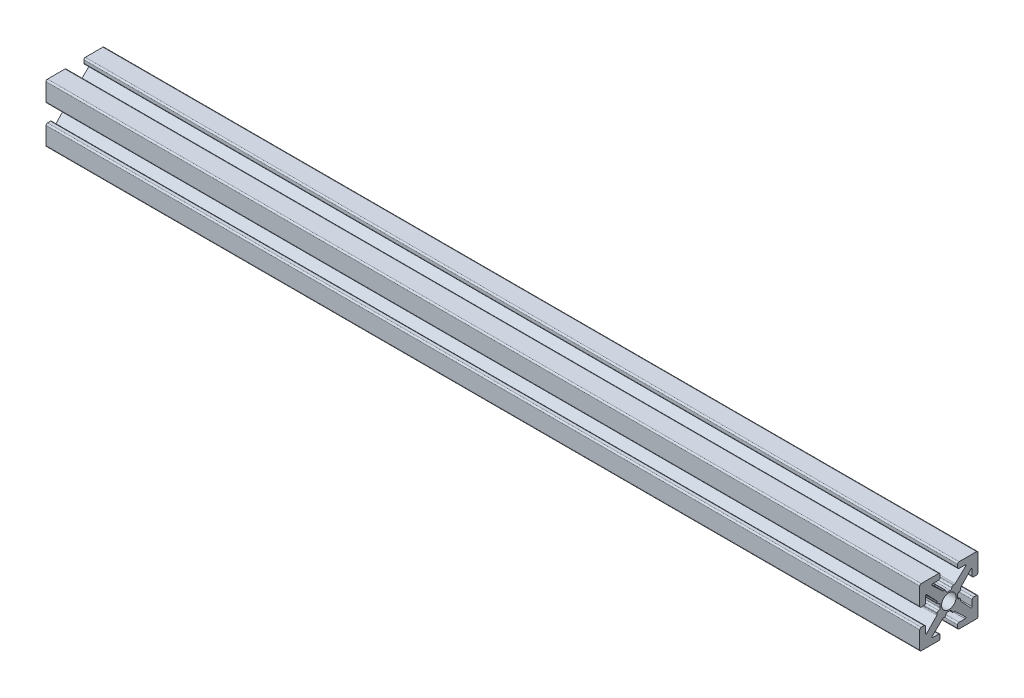
SolidWorks part; units mm, degrees
material "1060 Сплав"
ref_plane "Front Plane" through (0, 0, 0) normal (0, 0, 1) x (1, 0, 0)
ref_plane "Top Plane" through (0, 0, 0) normal (0, 1, 0) x (1, 0, 0)
ref_plane "Right Plane" through (0, 0, 0) normal (1, 0, 0) x (0, 0, -1)
sketch "Sketch1" plane through (0, 0, 0) normal (1, 0, 0) x (0, 0, -1)
  line L0 (0, 0) -> (0, 1.4948) construction
  line L1 (-0.2413, 1.4948) -> (0.2413, 1.4948)
  line L2 (5, 1.7526) -> (5, 4.746)
  line L3 (0.7493, 2.0028) -> (0.8899, 2.0028)
  line L4 (1.0639, 2.0718) -> (2.8908, 3.7899)
  line L5 (2.8038, 4.0094) -> (1.7526, 4.0094)
  line L6 (1.4986, 4.2634) -> (1.4986, 4.746)
  line L7 (1.7526, 5) -> (4.746, 5)
  line L8 (5, 5) -> (0, 0) construction
  line L9 (0, 0) -> (8.6271, 0) construction
  line L10 (0, 0) -> (0, 5) construction
  line L11 (4.2634, 1.4986) -> (4.746, 1.4986)
  line L12 (4.0094, 2.8038) -> (4.0094, 1.7526)
  line L13 (2.0718, 1.0639) -> (3.7899, 2.8908)
  line L14 (2.0028, 0.7493) -> (2.0028, 0.8899)
  line L15 (1.4948, -0.2413) -> (1.4948, 0.2413)
  line L16 (0, 0) -> (1.4948, 0) construction
  line L17 (-0.2413, -1.4948) -> (0.2413, -1.4948)
  line L18 (0.7493, -2.0028) -> (0.8899, -2.0028)
  line L19 (1.0639, -2.0718) -> (2.8908, -3.7899)
  line L20 (2.8038, -4.0094) -> (1.7526, -4.0094)
  line L21 (1.4986, -4.2634) -> (1.4986, -4.746)
  line L22 (1.7526, -5) -> (4.746, -5)
  line L23 (5, -1.7526) -> (5, -4.746)
  line L24 (4.2634, -1.4986) -> (4.746, -1.4986)
  line L25 (4.0094, -2.8038) -> (4.0094, -1.7526)
  line L26 (2.0718, -1.0639) -> (3.7899, -2.8908)
  line L27 (2.0028, -0.7493) -> (2.0028, -0.8899)
  line L28 (-0.7493, 2.0028) -> (-0.8899, 2.0028)
  line L29 (-1.0639, 2.0718) -> (-2.8908, 3.7899)
  line L30 (-2.8038, 4.0094) -> (-1.7526, 4.0094)
  line L31 (-1.4986, 4.2634) -> (-1.4986, 4.746)
  line L32 (-1.7526, 5) -> (-4.746, 5)
  line L33 (-5, 1.7526) -> (-5, 4.746)
  line L34 (-4.2634, 1.4986) -> (-4.746, 1.4986)
  line L35 (-4.0094, 2.8038) -> (-4.0094, 1.7526)
  line L36 (-2.0718, 1.0639) -> (-3.7899, 2.8908)
  line L37 (-2.0028, 0.7493) -> (-2.0028, 0.8899)
  line L38 (-1.4948, -0.2413) -> (-1.4948, 0.2413)
  line L39 (-2.0028, -0.7493) -> (-2.0028, -0.8899)
  line L40 (-2.0718, -1.0639) -> (-3.7899, -2.8908)
  line L41 (-4.0094, -2.8038) -> (-4.0094, -1.7526)
  line L42 (-4.2634, -1.4986) -> (-4.746, -1.4986)
  line L43 (-5, -1.7526) -> (-5, -4.746)
  line L44 (-1.7526, -5) -> (-4.746, -5)
  line L45 (-1.4986, -4.2634) -> (-1.4986, -4.746)
  line L46 (-2.8038, -4.0094) -> (-1.7526, -4.0094)
  line L47 (-1.0639, -2.0718) -> (-2.8908, -3.7899)
  line L48 (-0.7493, -2.0028) -> (-0.8899, -2.0028)
  arc A0 (2.8908, 3.7899) -> (2.8038, 4.0094) centre (2.8038, 3.8824) ccw
  arc A1 (0.4953, 1.7488) -> (0.7493, 2.0028) centre (0.7493, 1.7488) cw
  arc A2 (0.8899, 2.0028) -> (1.0639, 2.0718) centre (0.8899, 2.2568) ccw
  arc A3 (1.7526, 4.0094) -> (1.4986, 4.2634) centre (1.7526, 4.2634) cw
  arc A4 (1.4986, 4.746) -> (1.7526, 5) centre (1.7526, 4.746) cw
  arc A5 (0.2413, 1.4948) -> (0.4953, 1.7488) centre (0.2413, 1.7488) ccw
  arc A6 (4.746, 1.4986) -> (5, 1.7526) centre (4.746, 1.7526) ccw
  arc A7 (4.0094, 1.7526) -> (4.2634, 1.4986) centre (4.2634, 1.7526) ccw
  arc A8 (3.7899, 2.8908) -> (4.0094, 2.8038) centre (3.8824, 2.8038) cw
  arc A9 (2.0028, 0.8899) -> (2.0718, 1.0639) centre (2.2568, 0.8899) cw
  arc A10 (1.7488, 0.4953) -> (2.0028, 0.7493) centre (1.7488, 0.7493) ccw
  arc A11 (1.4948, 0.2413) -> (1.7488, 0.4953) centre (1.7488, 0.2413) cw
  arc A12 (0.2413, -1.4948) -> (0.4953, -1.7488) centre (0.2413, -1.7488) cw
  arc A13 (0.4953, -1.7488) -> (0.7493, -2.0028) centre (0.7493, -1.7488) ccw
  arc A14 (0.8899, -2.0028) -> (1.0639, -2.0718) centre (0.8899, -2.2568) cw
  arc A15 (2.8908, -3.7899) -> (2.8038, -4.0094) centre (2.8038, -3.8824) cw
  arc A16 (1.7526, -4.0094) -> (1.4986, -4.2634) centre (1.7526, -4.2634) ccw
  arc A17 (1.4986, -4.746) -> (1.7526, -5) centre (1.7526, -4.746) ccw
  arc A18 (4.746, -1.4986) -> (5, -1.7526) centre (4.746, -1.7526) cw
  arc A19 (4.0094, -1.7526) -> (4.2634, -1.4986) centre (4.2634, -1.7526) cw
  arc A20 (3.7899, -2.8908) -> (4.0094, -2.8038) centre (3.8824, -2.8038) ccw
  arc A21 (2.0028, -0.8899) -> (2.0718, -1.0639) centre (2.2568, -0.8899) ccw
  arc A22 (1.7488, -0.4953) -> (2.0028, -0.7493) centre (1.7488, -0.7493) cw
  arc A23 (1.4948, -0.2413) -> (1.7488, -0.4953) centre (1.7488, -0.2413) ccw
  arc A24 (-0.2413, 1.4948) -> (-0.4953, 1.7488) centre (-0.2413, 1.7488) cw
  arc A25 (-0.4953, 1.7488) -> (-0.7493, 2.0028) centre (-0.7493, 1.7488) ccw
  arc A26 (-0.8899, 2.0028) -> (-1.0639, 2.0718) centre (-0.8899, 2.2568) cw
  arc A27 (-2.8908, 3.7899) -> (-2.8038, 4.0094) centre (-2.8038, 3.8824) cw
  arc A28 (-1.7526, 4.0094) -> (-1.4986, 4.2634) centre (-1.7526, 4.2634) ccw
  arc A29 (-1.4986, 4.746) -> (-1.7526, 5) centre (-1.7526, 4.746) ccw
  arc A30 (-4.746, 1.4986) -> (-5, 1.7526) centre (-4.746, 1.7526) cw
  arc A31 (-4.0094, 1.7526) -> (-4.2634, 1.4986) centre (-4.2634, 1.7526) cw
  arc A32 (-3.7899, 2.8908) -> (-4.0094, 2.8038) centre (-3.8824, 2.8038) ccw
  arc A33 (-2.0028, 0.8899) -> (-2.0718, 1.0639) centre (-2.2568, 0.8899) ccw
  arc A34 (-1.7488, 0.4953) -> (-2.0028, 0.7493) centre (-1.7488, 0.7493) cw
  arc A35 (-1.4948, 0.2413) -> (-1.7488, 0.4953) centre (-1.7488, 0.2413) ccw
  arc A36 (-1.4948, -0.2413) -> (-1.7488, -0.4953) centre (-1.7488, -0.2413) cw
  arc A37 (-1.7488, -0.4953) -> (-2.0028, -0.7493) centre (-1.7488, -0.7493) ccw
  arc A38 (-2.0028, -0.8899) -> (-2.0718, -1.0639) centre (-2.2568, -0.8899) cw
  arc A39 (-3.7899, -2.8908) -> (-4.0094, -2.8038) centre (-3.8824, -2.8038) cw
  arc A40 (-4.0094, -1.7526) -> (-4.2634, -1.4986) centre (-4.2634, -1.7526) ccw
  arc A41 (-4.746, -1.4986) -> (-5, -1.7526) centre (-4.746, -1.7526) ccw
  arc A42 (-1.4986, -4.746) -> (-1.7526, -5) centre (-1.7526, -4.746) cw
  arc A43 (-1.7526, -4.0094) -> (-1.4986, -4.2634) centre (-1.7526, -4.2634) cw
  arc A44 (-2.8908, -3.7899) -> (-2.8038, -4.0094) centre (-2.8038, -3.8824) ccw
  arc A45 (-0.8899, -2.0028) -> (-1.0639, -2.0718) centre (-0.8899, -2.2568) ccw
  arc A46 (-0.4953, -1.7488) -> (-0.7493, -2.0028) centre (-0.7493, -1.7488) cw
  arc A47 (-0.2413, -1.4948) -> (-0.4953, -1.7488) centre (-0.2413, -1.7488) ccw
  arc A48 (-4.746, 5) -> (-5, 4.746) centre (-4.746, 4.746) ccw
  arc A49 (-5, -4.746) -> (-4.746, -5) centre (-4.746, -4.746) ccw
  arc A50 (4.746, -5) -> (5, -4.746) centre (4.746, -4.746) ccw
  arc A51 (4.746, 5) -> (5, 4.746) centre (4.746, 4.746) cw
  point P14 (3.1242, 4.0094)
  point P19 (0.9906, 2.0028)
  point P150 (0, -1.4948)
  point P152 (-5, 5)
  point P155 (-5, -5)
  point P158 (5, -5)
  dimension "D10" = 0.127
  dimension "D11" = 0.254
  dimension "D2" = 0.254
  dimension "D1" = 10
  dimension "D3" = 2.9972
  dimension "D4" = 0.508
  dimension "D5" = 2.9972
  dimension "D6" = 0.9906
  dimension "D7" = 1.6256
  dimension "D8" = 1.9812
  dimension "D9" = 0.9906
extrude "Estrusione-Estrusione1" add sketch "Sketch1" along normal blind 150 contours L36 A32 L35 A31 L34 A30 L33 A48 L32 A29 L31 A28 L30 A27 L29 A26 L28 A25 A24 L1 A5 A1 L3 A2 L4 A0 L5 A3 L6 A4 L7 A51 L2 A6 L11 A7 L12 A8 L13 A9 L14 A10 A11 L15 A23 A22 L27 A21 L26 A20 L25 A19 L24 A18 L23 A50 L22 A17 L21 A16 L20 A15 L19 A14 L18 A13 A12 L17 A47 A46 L48 A45 L47 A44 L46 A43 L45 A42 L44 A49 L43 A41 L42 A40 L41 A39 L40 A38 L39 A37 A36 L38 A35 A34 L37 A33
hole_wizard "Foro filettato M3x0.5-1" positions "Schizzo2" profile "Schizzo1" tap size "M3x0.5" standard "Ansi Metric" end condition through all
sketch "Schizzo2" plane through (0, 0, 0) normal (-1, 0, 0) x (0, 0, 1)
  point P0 (0, 0)
sketch "Schizzo1" plane through (0, 0, 0) normal (0, 1, 0) x (0, 0, 1)
  line L0 (0, 0) -> (0, 150)
  line L1 (0, 150) -> (1.25, 150)
  line L2 (1.25, 150) -> (1.25, 0)
  line L5 (1.25, 0) -> (0, 0)
  line L11 (0, -6.35) -> (0, 107.95) construction
  dimension "Thread Major Dia." = 2.5
  dimension "Thru Tap Drill Depth" = 150
equation "\"camera plate width\"=220"
equation "\"camera plate length\"=220"
equation "\"camera height\"= 100"
equation "\"D1@Estrusione-Estrusione1\"=150"
equation "\"zero height\"= 100"
